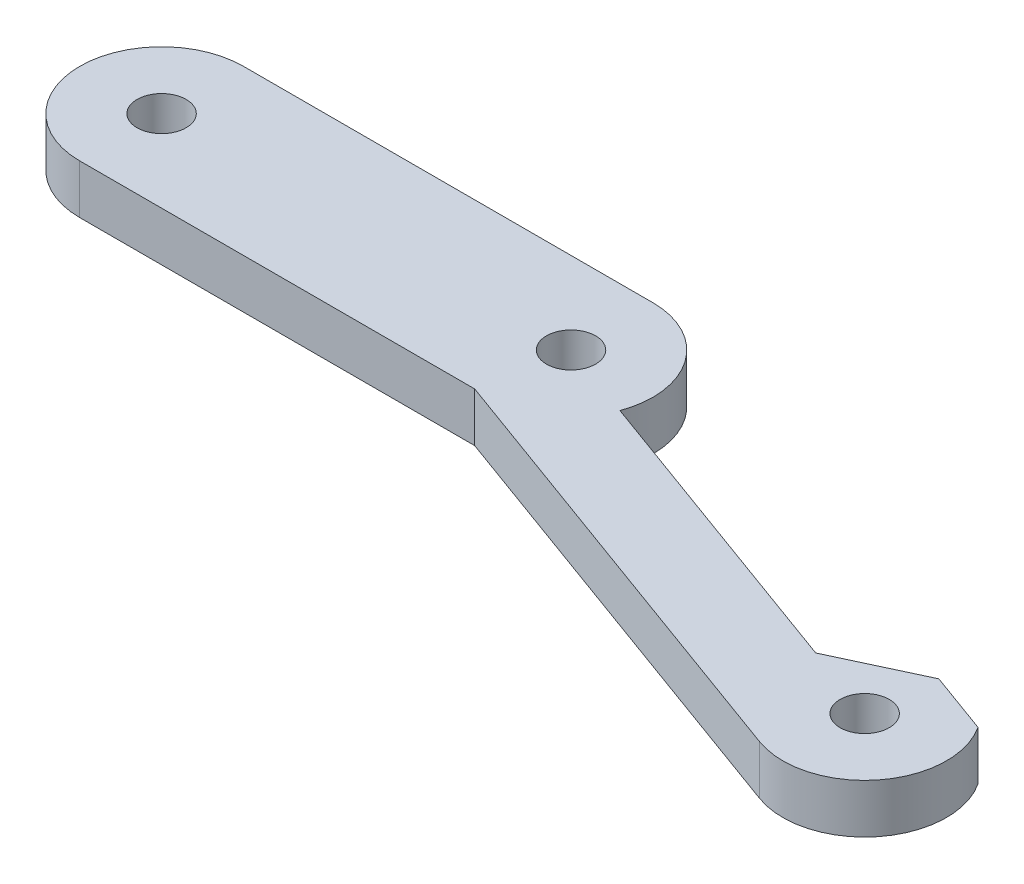
SolidWorks part; units mm, degrees
ref_plane "Front Plane" through (0, 0, 0) normal (0, 0, 1) x (1, 0, 0)
ref_plane "Top Plane" through (0, 0, 0) normal (0, 1, 0) x (1, 0, 0)
ref_plane "Right Plane" through (0, 0, 0) normal (1, 0, 0) x (0, 0, -1)
sketch "Sketch1" plane through (0, 0, 0) normal (0, 1, 0) x (1, 0, 0)
  line L0 (0, 0) -> (25, 0) construction
  line L5 (0, 5) -> (25, 5)
  line L6 (0, -5) -> (25, -5)
  line L7 (25, 0) -> (53.1908, -10.2606) construction
  line L8 (26.7101, 4.6985) -> (54.9009, -5.5621)
  line L9 (23.2899, -4.6985) -> (51.4807, -14.9591)
  arc A0 (0, 5) -> (0, -5) centre (0, 0) ccw
  arc A1 (25, -5) -> (25, 5) centre (25, 0) ccw
  arc A2 (26.7101, 4.6985) -> (23.2899, -4.6985) centre (25, 0) ccw
  arc A3 (51.4807, -14.9591) -> (54.9009, -5.5621) centre (53.1908, -10.2606) ccw
  circle A4 centre (0, 0) radius 1.5
  circle A5 centre (25, 0) radius 1.5
  circle A6 centre (53.1908, -10.2606) radius 1.5
  point P2 (12.5, 0)
  point P9 (39.0954, -5.1303)
  dimension "D6" = 3
  dimension "D7" = 3
  dimension "D8" = 3
  dimension "D1" = 25
  dimension "D2" = 30
  dimension "D3" = 160
  dimension "D4" = 10
  dimension "D5" = 10
extrude "Boss-Extrude1" add sketch "Sketch1" along normal blind 3 contours L9 A3 L8 A1 L6 A6 | A5 | A4
sketch "Sketch2" plane through (0, 3, 0) normal (0, 1, 0) x (1, 0, 0)
  line L0 (0, -5) -> (24.1184, -5) construction
  line L1 (63.9238, -9.9104) -> (45.8728, -3.3404)
  line L2 (24.1184, -5) -> (51.4807, -14.9591) construction
  line L3 (53.1908, -10.2606) -> (25, 0) construction
  line L4 (48.4923, -8.5505) -> (53.6192, -6.1598)
  line L5 (48.4923, -8.5505) -> (29.6985, -1.7101)
  circle A0 centre (25, 0) radius 5
  dimension "D1" = 9
  dimension "D2" = 45
  dimension "D3" = 5
extrude "Cut-Extrude1" cut sketch "Sketch2" against normal blind 10
